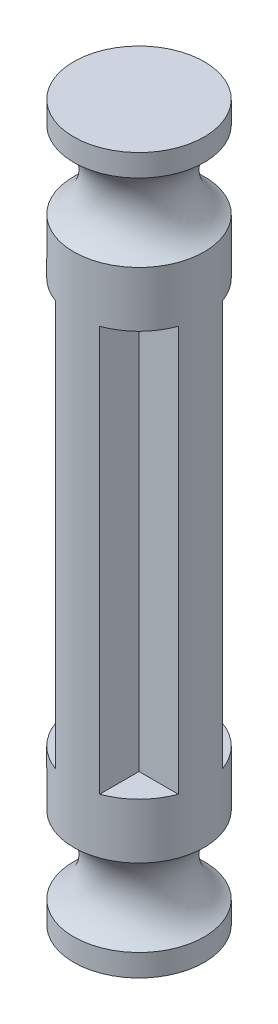
SolidWorks part; units mm, degrees
ref_plane "前视基准面" through (0, 0, 0) normal (0, 0, 1) x (1, 0, 0)
ref_plane "上视基准面" through (0, 0, 0) normal (0, 1, 0) x (1, 0, 0)
ref_plane "右视基准面" through (0, 0, 0) normal (1, 0, 0) x (0, 0, -1)
sketch "草图1" plane through (0, 0, 0) normal (0, 1, 0) x (1, 0, 0)
  line L0 (1, 1) -> (1, 2.7753)
  line L7 (1, 1) -> (2.7753, 1)
  line L8 (1, -1) -> (2.7753, -1)
  line L9 (1, -1) -> (1, -2.7753)
  line L10 (-1, -1) -> (-1, -2.7753)
  line L11 (-1, -1) -> (-2.7753, -1)
  line L12 (-1, 1) -> (-2.7753, 1)
  line L13 (-1, 1) -> (-1, 2.7753)
  arc A0 (-2.7753, 1) -> (-2.7753, -1) centre (0, 0) ccw
  arc A1 (-1, -2.7753) -> (1, -2.7753) centre (0, 0) ccw
  arc A2 (2.7753, -1) -> (2.7753, 1) centre (0, 0) ccw
  arc A3 (1, 2.7753) -> (-1, 2.7753) centre (0, 0) ccw
  dimension "D1" = 5.9
  dimension "D2" = 2
  dimension "D3" = 2
  dimension "D4" = 2
  dimension "D5" = 2
  dimension "D6" = 1
  dimension "D7" = 1
  dimension "D8" = 1
  dimension "D9" = 1
extrude "凸台-拉伸2" add sketch "草图1" along normal blind 18.32
sketch "草图3" plane through (0, 0, 0) normal (1, 0, 0) x (0, 0, -1)
  line L0 (0, 18.32) -> (0, 25.32)
  line L1 (1, 18.32) -> (-1, 18.32) construction
  line L2 (0, 25.32) -> (2.95, 25.32)
  line L3 (0, 18.32) -> (2.95, 18.32)
  line L4 (2.95, 18.32) -> (2.95, 20.82)
  line L5 (2.95, 25.32) -> (2.95, 24.32)
  line L6 (0, 0) -> (0, -7)
  line L7 (0, -7) -> (2.95, -7)
  line L8 (0, 0) -> (2.95, 0)
  line L9 (2.95, 0) -> (2.95, -2.5)
  line L10 (2.95, -7) -> (2.95, -6)
  arc A0 (2.95, 24.32) -> (2.95, 20.82) centre (3.9182, 22.57) ccw
  arc A1 (2.95, -2.5) -> (2.95, -6) centre (3.9182, -4.25) ccw
  dimension "D5" = 1
  dimension "D4" = 2
  dimension "D9" = 2
  dimension "D1" = 2.95
  dimension "D2" = 7
  dimension "D3" = 2.5
  dimension "D6" = 7
  dimension "D7" = 2.5
  dimension "D8" = 1
revolve "旋转3" add sketch "草图3" angle 360 about L6
